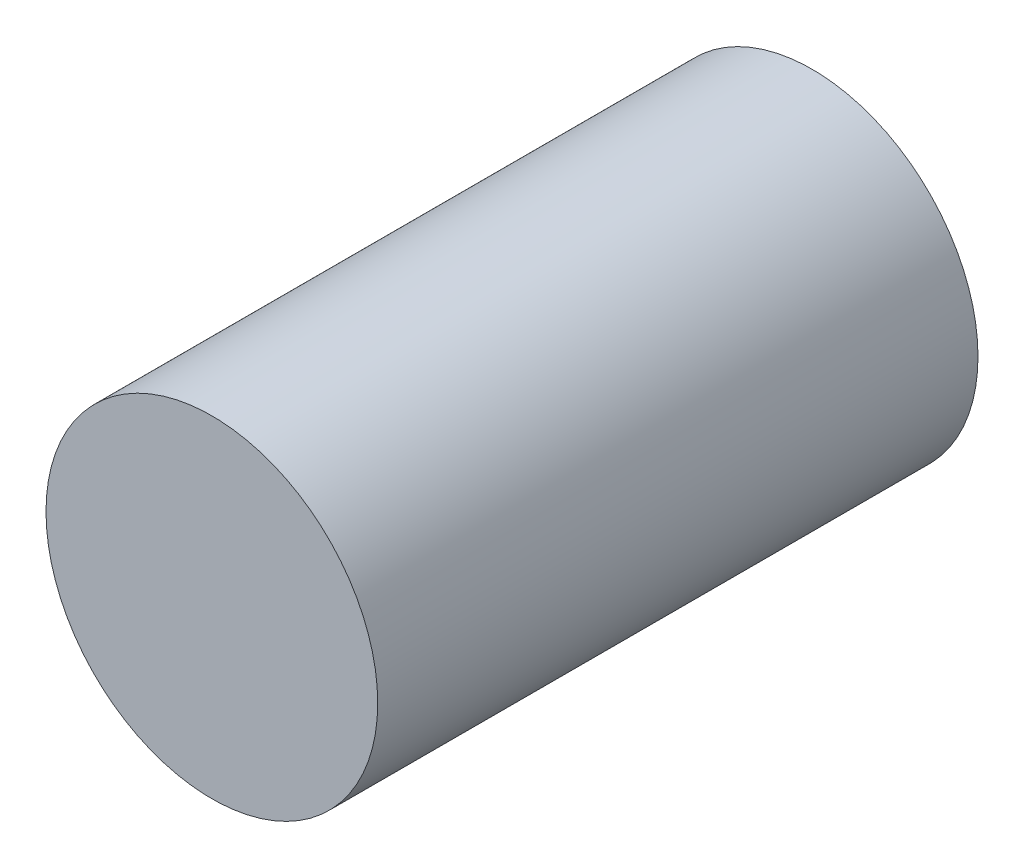
SolidWorks part; units mm, degrees
material "Natural Rubber"
ref_plane "Front Plane" through (0, 0, 0) normal (0, 0, 1) x (1, 0, 0)
ref_plane "Top Plane" through (0, 0, 0) normal (0, 1, 0) x (1, 0, 0)
ref_plane "Right Plane" through (0, 0, 0) normal (1, 0, 0) x (0, 0, -1)
sketch "Sketch1" plane through (0, 0, 0) normal (0, 0, 1) x (1, 0, 0)
  circle A0 centre (0, 0) radius 2.625
  dimension "D1" = 5.25
extrude "Boss-Extrude1" add sketch "Sketch1" along normal blind 9.5
